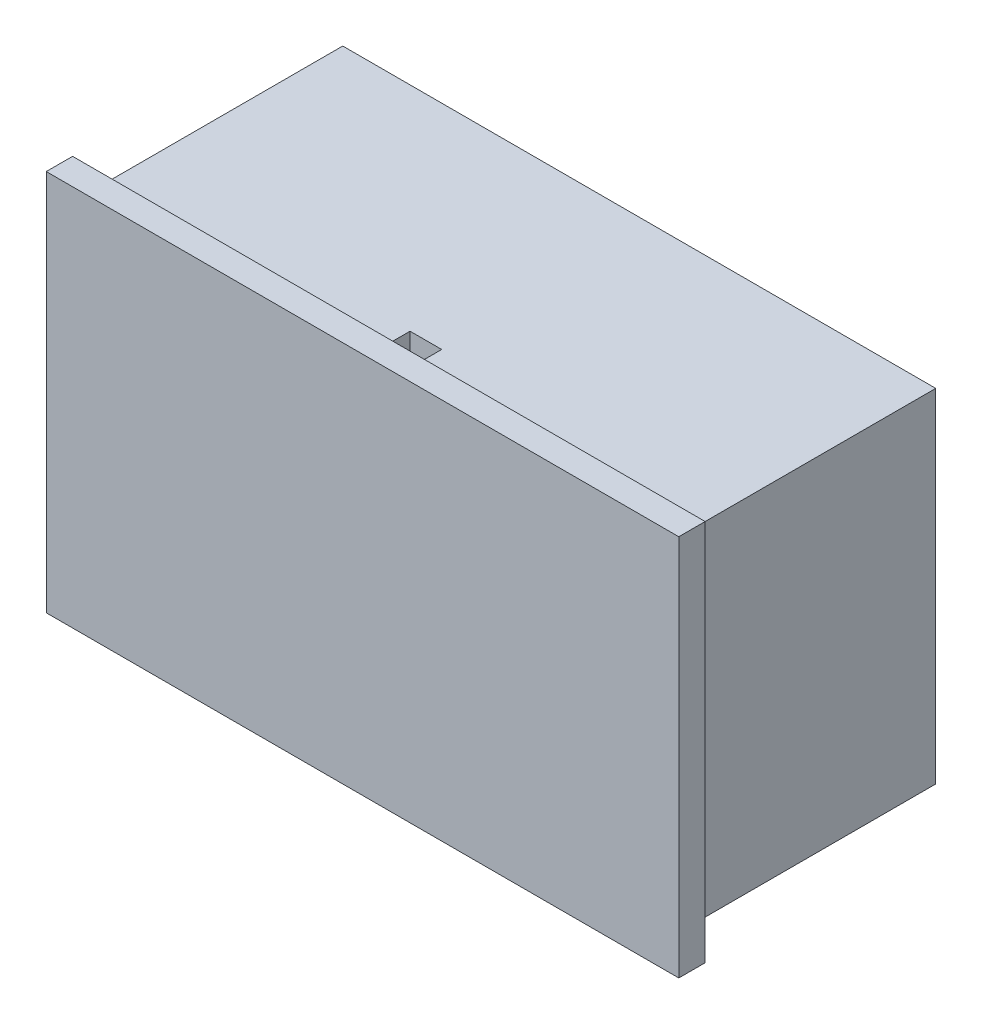
SolidWorks part; units mm, degrees
ref_plane "Front Plane" through (0, 0, 0) normal (0, 0, 1) x (1, 0, 0)
ref_plane "Top Plane" through (0, 0, 0) normal (0, 1, 0) x (1, 0, 0)
ref_plane "Right Plane" through (0, 0, 0) normal (1, 0, 0) x (0, 0, -1)
sketch "Sketch1" plane through (0, 0, 0) normal (0, 1, 0) x (1, 0, 0)
  line L1 (22.5, -9.5) -> (-22.5, -9.5)
  line L2 (22.5, -9.5) -> (22.5, 9.5)
  line L3 (22.5, 9.5) -> (-22.5, 9.5)
  line L4 (-22.5, -9.5) -> (-22.5, 9.5)
  line L5 (22.5, -9.5) -> (-22.5, 9.5) construction
  line L6 (22.5, 9.5) -> (-22.5, -9.5) construction
  point P0 (0, 0)
  dimension "D1" = 45
  dimension "D2" = 19
extrude "Boss-Extrude1" add sketch "Sketch1" along normal blind 26
sketch "Sketch2" plane through (0, 0, 9.5) normal (0, 0, 1) x (1, 0, 0)
  line L0 (-24, 27.5) -> (-24, -1.5)
  line L1 (-24, -1.5) -> (24, -1.5)
  line L2 (24, -1.5) -> (24, 27.5)
  line L3 (24, 27.5) -> (-24, 27.5)
  line L4 (-22.5, 26) -> (22.5, 26) construction
  line L7 (-22.5, 26) -> (-22.5, 0) construction
  line L8 (22.5, 26) -> (22.5, 0) construction
  dimension "D1" = 29
  dimension "D2" = 1.5
  dimension "D3" = 1.5
  dimension "D4" = 1.5
extrude "Boss-Extrude2" add sketch "Sketch2" along normal blind 2
sketch "Sketch3" plane through (0, 26, 0) normal (0, 1, 0) x (1, 0, 0)
  line L1 (1.1968, -8.289) -> (-1.2032, -8.289)
  line L2 (1.1968, -8.289) -> (1.1968, -6.689)
  line L3 (1.1968, -6.689) -> (-1.2032, -6.689)
  line L4 (-1.2032, -8.289) -> (-1.2032, -6.689)
  line L5 (1.1968, -8.289) -> (-1.2032, -6.689) construction
  line L6 (1.1968, -6.689) -> (-1.2032, -8.289) construction
  point P0 (-0.0032, -7.489)
  dimension "D1" = 1.6
  dimension "D2" = 2.4
extrude "Cut-Extrude1" cut sketch "Sketch3" against normal blind 2
